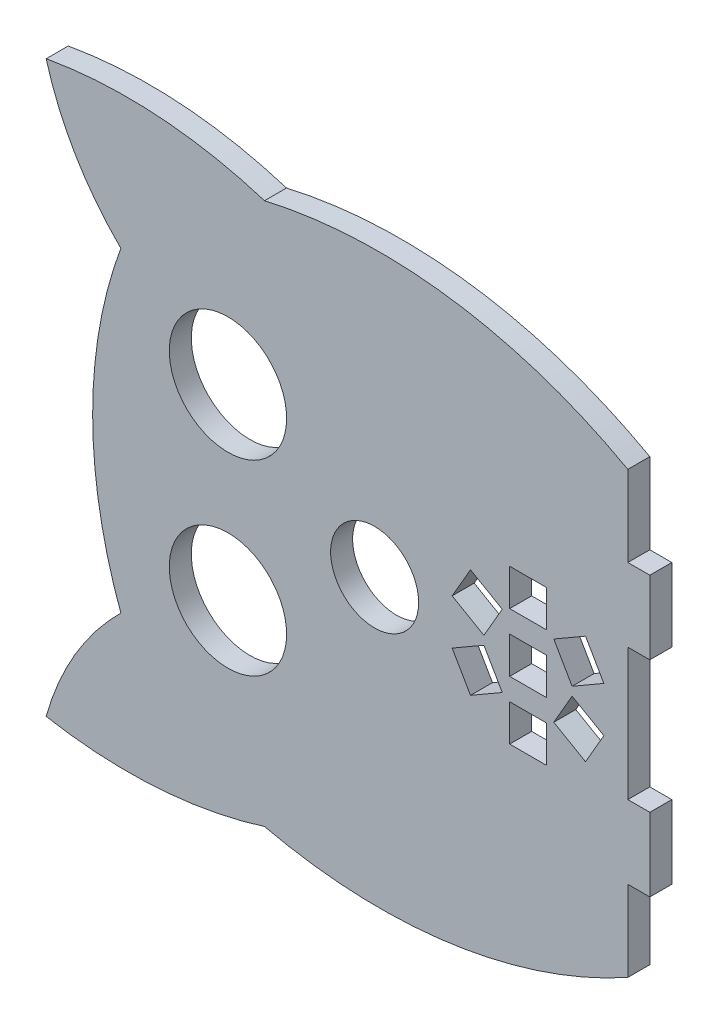
SolidWorks part; units mm, degrees
ref_plane "Front Plane" through (0, 0, 0) normal (0, 0, 1) x (1, 0, 0)
ref_plane "Top Plane" through (0, 0, 0) normal (0, 1, 0) x (1, 0, 0)
ref_plane "Right Plane" through (0, 0, 0) normal (1, 0, 0) x (0, 0, -1)
sketch "Sketch2" plane through (0, 0, 0) normal (0, 0, 1) x (1, 0, 0)
  line L0 (81.0321, 50.1813) -> (81.0321, 60.1813)
  line L1 (81.0321, 60.1813) -> (78.0321, 60.1813)
  line L2 (78.0321, 60.1813) -> (78.0321, 71.1813)
  line L15 (78.0321, 11.1813) -> (78.0321, 22.1813)
  line L16 (78.0321, 22.1813) -> (81.0321, 22.1813)
  line L17 (81.0321, 22.1813) -> (81.0321, 32.1813)
  line L18 (81.0321, 32.1813) -> (78.0321, 32.1813)
  line L19 (78.0321, 32.1813) -> (78.0321, 50.1813)
  line L20 (78.0321, 50.1813) -> (81.0321, 50.1813)
  line L21 (61.923, 43.6813) -> (61.923, 38.6813)
  line L22 (61.923, 38.6813) -> (66.923, 38.6813)
  line L23 (66.923, 38.6813) -> (66.923, 43.6813)
  line L24 (66.923, 43.6813) -> (61.923, 43.6813)
  line L25 (61.923, 35.6813) -> (61.923, 30.6813)
  line L26 (61.923, 30.6813) -> (66.923, 30.6813)
  line L27 (66.923, 30.6813) -> (66.923, 35.6813)
  line L28 (66.923, 35.6813) -> (61.923, 35.6813)
  line L29 (72.2663, 48.5964) -> (67.9362, 46.0964)
  line L30 (67.9362, 46.0964) -> (70.4362, 41.7662)
  line L31 (70.4362, 41.7662) -> (74.7663, 44.2662)
  line L32 (74.7663, 44.2662) -> (72.2663, 48.5964)
  line L33 (67.9362, 36.2662) -> (72.2663, 33.7662)
  line L34 (72.2663, 33.7662) -> (74.7663, 38.0964)
  line L35 (74.7663, 38.0964) -> (70.4362, 40.5964)
  line L36 (70.4362, 40.5964) -> (67.9362, 36.2662)
  line L37 (61.923, 51.6813) -> (61.923, 46.6813)
  line L38 (61.923, 46.6813) -> (66.923, 46.6813)
  line L39 (66.923, 46.6813) -> (66.923, 51.6813)
  line L40 (66.923, 51.6813) -> (61.923, 51.6813)
  line L41 (56.5798, 33.7662) -> (60.9099, 36.2662)
  line L42 (60.9099, 36.2662) -> (58.4099, 40.5964)
  line L43 (58.4099, 40.5964) -> (54.0798, 38.0964)
  line L44 (54.0798, 38.0964) -> (56.5798, 33.7662)
  line L45 (60.9099, 46.0964) -> (56.5798, 48.5964)
  line L46 (56.5798, 48.5964) -> (54.0798, 44.2662)
  line L47 (54.0798, 44.2662) -> (58.4099, 41.7662)
  line L48 (58.4099, 41.7662) -> (60.9099, 46.0964)
  line L49 (78.0321, 41.1813) -> (23.507, 41.1813) construction
  circle A0 centre (23.507, 53.9313) radius 8
  circle A1 centre (43.507, 41.1813) radius 6
  circle A2 centre (23.507, 28.4313) radius 8
  arc A32 (28.4945, 78.1348) -> (78.0321, 71.1813) centre (44.2116, 10.1718) cw
  arc A33 (28.4945, 4.2279) -> (78.0321, 11.1813) centre (44.2116, 72.1908) ccw
  arc A34 (28.4945, 78.1348) -> (-1.2792, 80.0172) centre (9.7799, 18.5334) ccw
  arc A35 (-1.2792, 80.0172) -> (8.9024, 62.7188) centre (36.2125, 90.4388) ccw
  arc A36 (8.9024, 62.7188) -> (8.9024, 19.6438) centre (67.2985, 41.1813) ccw
  arc A37 (28.4945, 4.2279) -> (-1.2792, 2.3455) centre (9.7799, 63.8292) cw
  arc A38 (-1.2792, 2.3455) -> (8.9024, 19.6438) centre (36.2125, -8.0762) cw
  dimension "D2" = 12.75
  dimension "D3" = 12.75
  dimension "D1" = 11
extrude "Boss-Extrude1" add sketch "Sketch2" along normal blind 3
